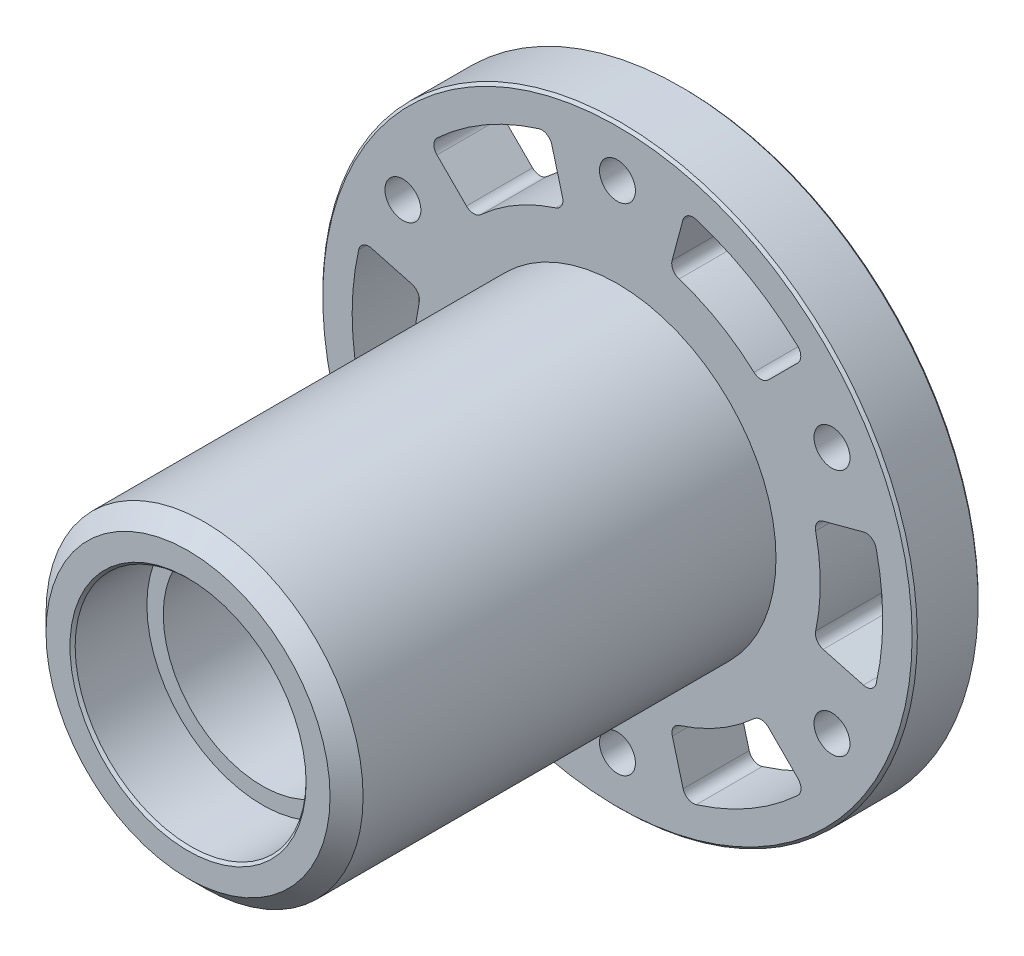
SolidWorks part; units mm, degrees
ref_plane "Front Plane" through (0, 0, 0) normal (0, 0, 1) x (1, 0, 0)
ref_plane "Top Plane" through (0, 0, 0) normal (0, 1, 0) x (1, 0, 0)
ref_plane "Right Plane" through (0, 0, 0) normal (1, 0, 0) x (0, 0, -1)
ref_plane "Plane1" through (0, 0, 0) normal (0, -1, 0) x (1, 0, 0)
sketch "Sketch1" plane through (0, 0, 0) normal (0, -1, 0) x (1, 0, 0)
  line L0 (28.575, 3.175) -> (0, 3.175)
  line L1 (0, 3.175) -> (0, -3.175)
  line L2 (0, -3.175) -> (28.575, -3.175)
  line L3 (28.575, -3.175) -> (28.575, 3.175)
  line L4 (0, 3.175) -> (0, -3.175) construction
revolve "Revolve1" add sketch "Sketch1" angle 360 about L4
sketch "Sketch2" plane through (0, 0, -3.175) normal (0, 0, -1) x (-1, 0, 0)
  line L0 (13.8245, 13.7526) -> (18.0671, 17.9953)
  line L1 (6.5753, 24.6377) -> (5.0224, 18.8421)
  arc A0 (18.0671, 17.9953) -> (6.5753, 24.6377) centre (0, 0) ccw
  arc A1 (5.0224, 18.8421) -> (13.8245, 13.7526) centre (0, 0) cw
extrude "Cut-Extrude1" cut sketch "Sketch2" against normal through all
sketch "Sketch3" plane through (0, 0, -3.175) normal (0, 0, -1) x (-1, 0, 0)
  line L0 (-4.9979, 18.8486) -> (-6.5508, 24.6442)
  line L1 (-18.0492, 18.0133) -> (-13.8065, 13.7706)
  arc A0 (-13.8065, 13.7706) -> (-4.9979, 18.8486) centre (0, 0) cw
  arc A1 (-6.5508, 24.6442) -> (-18.0492, 18.0133) centre (0, 0) ccw
extrude "Cut-Extrude2" cut sketch "Sketch3" against normal through all
sketch "Sketch4" plane through (0, 0, -3.175) normal (0, 0, -1) x (-1, 0, 0)
  line L0 (-18.8223, 5.096) -> (-24.6179, 6.6489)
  line L1 (-24.6245, -6.6244) -> (-18.829, -5.0715)
  arc A0 (-18.829, -5.0715) -> (-18.8223, 5.096) centre (0, 0) cw
  arc A1 (-24.6179, 6.6489) -> (-24.6245, -6.6244) centre (0, 0) ccw
extrude "Cut-Extrude3" cut sketch "Sketch4" against normal through all
sketch "Sketch5" plane through (0, 0, -3.175) normal (0, 0, -1) x (-1, 0, 0)
  line L0 (-6.5753, -24.6377) -> (-5.0224, -18.8421)
  line L1 (-13.8245, -13.7526) -> (-18.0671, -17.9953)
  arc A0 (-5.0224, -18.8421) -> (-13.8245, -13.7526) centre (0, 0) cw
  arc A1 (-18.0671, -17.9953) -> (-6.5753, -24.6377) centre (0, 0) ccw
extrude "Cut-Extrude4" cut sketch "Sketch5" against normal through all
sketch "Sketch6" plane through (0, 0, -3.175) normal (0, 0, -1) x (-1, 0, 0)
  line L0 (18.0492, -18.0133) -> (13.8065, -13.7706)
  line L1 (4.9979, -18.8486) -> (6.5508, -24.6442)
  arc A0 (6.5508, -24.6442) -> (18.0492, -18.0133) centre (0, 0) ccw
  arc A1 (13.8065, -13.7706) -> (4.9979, -18.8486) centre (0, 0) cw
extrude "Cut-Extrude5" cut sketch "Sketch6" against normal through all
sketch "Sketch7" plane through (0, 0, 3.175) normal (0, 0, 1) x (1, 0, 0)
  line L0 (-18.829, 5.0715) -> (-24.6245, 6.6244)
  line L1 (-24.6179, -6.6489) -> (-18.8223, -5.096)
  arc A0 (-24.6245, 6.6244) -> (-24.6179, -6.6489) centre (0, 0) ccw
  arc A1 (-18.8223, -5.096) -> (-18.829, 5.0715) centre (0, 0) cw
extrude "Cut-Extrude6" cut sketch "Sketch7" against normal through all
sketch "Sketch8" plane through (0, 0, 3.175) normal (0, 0, 1) x (1, 0, 0)
  circle A0 centre (0, 0) radius 15.24
extrude "Boss-Extrude1" add sketch "Sketch8" along normal blind 41.275
sketch "Sketch9" plane through (0, 0, 0) normal (0, -1, 0) x (1, 0, 0)
  line L0 (11.0998, 44.45) -> (0, 44.45)
  line L1 (0, 44.45) -> (0, -3.175)
  line L2 (0, -3.175) -> (11.0998, -3.175)
  line L3 (11.0998, -3.175) -> (11.0998, 3.9688)
  line L4 (11.0998, 3.9688) -> (9.525, 3.9688)
  line L5 (9.525, 3.9688) -> (9.525, 37.3062)
  line L6 (9.525, 37.3062) -> (11.0998, 37.3062)
  line L7 (11.0998, 37.3062) -> (11.0998, 44.45)
  line L8 (0, 44.45) -> (0, -3.175) construction
revolve "Cut-Revolve1" cut sketch "Sketch9" angle 360 about L8
hole_wizard "M3 Clearance Hole1" positions "Sketch11" profile "Sketch10" hole size "M3" standard "ANSI Metric"
sketch "Sketch11" plane through (0, 0, -3.175) normal (0, 0, -1) x (-1, 0, 0)
  point P0 (-20.6222, 11.9063)
  point P1 (-20.6222, -11.9062)
  point P2 (0, -23.8125)
  point P3 (20.6222, -11.9063)
  point P4 (20.6222, 11.9062)
  point P5 (0, 23.8125)
sketch "Sketch10" plane through (20.6222, 11.9063, -3.175) normal (1, 0, 0) x (0, 1, 0)
  line L0 (0, 0) -> (0, 47.625)
  line L1 (0, 47.625) -> (1.7272, 47.625)
  line L2 (1.7272, 47.625) -> (1.7272, 0)
  line L5 (1.7272, 0) -> (0, 0)
  line L11 (0, -6.35) -> (0, 107.95) construction
  dimension "Thru Hole Dia." = 3.4544
  dimension "Thru Hole Depth" = 47.625
chamfer "Chamfer1" distance 0.25 angle 45 4 edges at (-28.575, 0, -3.175) (-11.0998, 0, -3.175) (-11.0998, 0, 44.45) (-28.575, 0, 3.175)
chamfer "Chamfer2" distance 1.5875 angle 45 1 edges at (15.24, 0, 44.45)
fillet "Fillet1" radius 1 24 edges at (24.6179, 6.6489, 0) (-6.5753, 24.6377, 0) (4.9979, 18.8486, 0) (-24.6179, -6.6489, 0) (18.829, -5.0715, 0) (-24.6245, 6.6244, 0) (13.8065, 13.7706, 0) (-18.829, 5.0715, 0) (-18.0671, 17.9953, 0) (-18.8223, -5.096, 0) (24.6245, -6.6244, 0) (-4.9979, -18.8486, 0) (18.8223, 5.096, 0) (-6.5508, -24.6442, 0) (18.0492, 18.0133, 0) (-13.8065, -13.7706, 0) (6.5508, 24.6442, 0) (-18.0492, -18.0133, 0) (-13.8245, 13.7526, 0) (6.5753, -24.6377, 0) (-5.0224, 18.8421, 0) (18.0671, -17.9953, 0) (13.8245, -13.7526, 0) (5.0224, -18.8421, 0)
